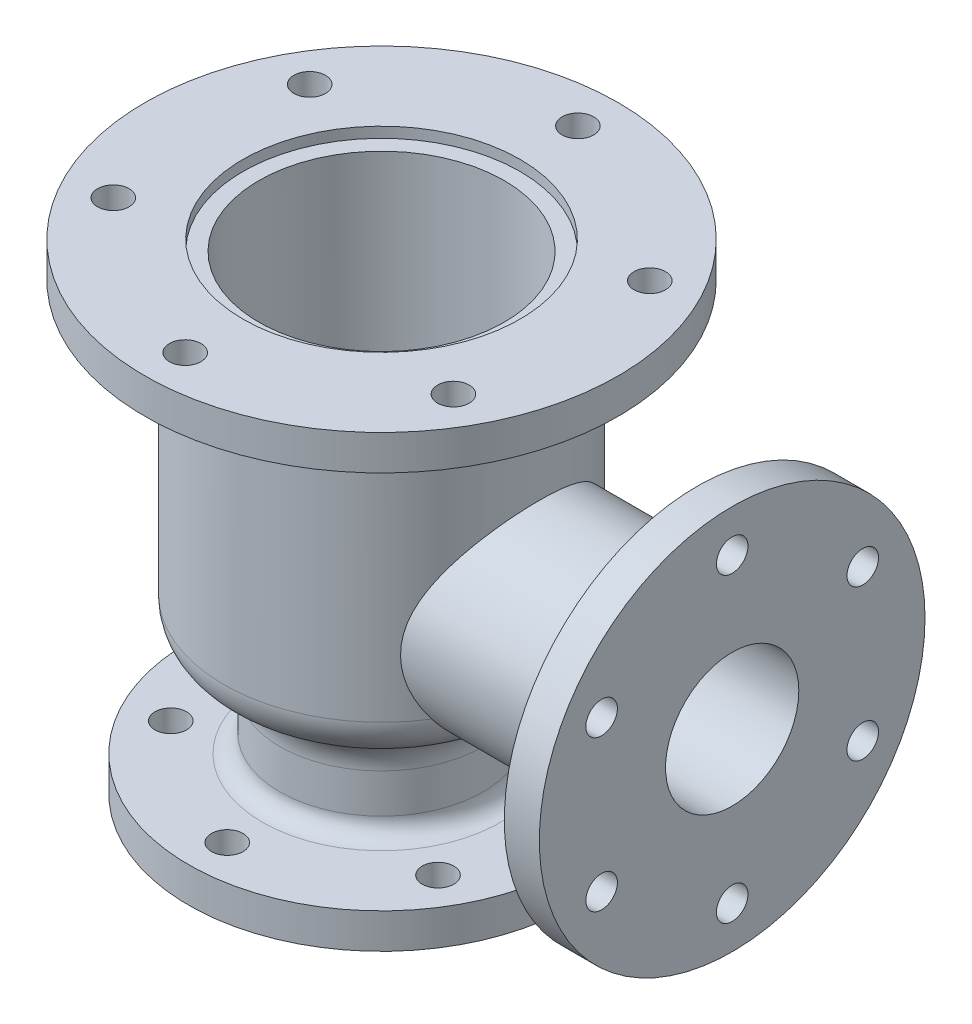
SolidWorks part; units mm, degrees
material "Plain Carbon Steel"
ref_plane "Front Plane" through (0, 0, 0) normal (0, 0, 1) x (1, 0, 0)
ref_plane "Top Plane" through (0, 0, 0) normal (0, 1, 0) x (1, 0, 0)
ref_plane "Right Plane" through (0, 0, 0) normal (1, 0, 0) x (0, 0, -1)
sketch "Sketch1" plane through (0, 0, 0) normal (0, 0, 1) x (1, 0, 0)
  line L0 (0, 0) -> (0, 279.8352) construction
  line L1 (38, 0) -> (110, 0)
  line L2 (110, 0) -> (110, 20)
  line L3 (110, 20) -> (58, 20)
  line L4 (58, 20) -> (58, 74)
  line L5 (90, 74) -> (90, 254)
  line L6 (90, 254) -> (135, 254)
  line L7 (135, 254) -> (135, 274)
  line L8 (135, 274) -> (79, 274)
  line L9 (79, 274) -> (79, 268)
  line L10 (79, 268) -> (70, 268)
  line L11 (70, 268) -> (70, 106)
  line L12 (60, 98) -> (60, 88)
  line L13 (60, 88) -> (46, 88)
  line L14 (46, 88) -> (46, 34)
  line L15 (46, 34) -> (38, 34)
  line L16 (38, 34) -> (38, 0)
  line L17 (58, 74) -> (90, 74)
  line L18 (60, 98) -> (62, 98)
  arc A0 (62, 98) -> (70, 106) centre (62, 106) ccw
  point P9 (70, 98)
  dimension "D4" = 180
  dimension "D6" = 180
  dimension "D7" = 8
  dimension "D1" = 220
  dimension "D2" = 20
  dimension "D3" = 116
  dimension "D5" = 54
  dimension "D9" = 270
  dimension "D10" = 20
  dimension "D11" = 158
  dimension "D12" = 6
  dimension "D13" = 140
  dimension "D14" = 170
  dimension "D16" = 10
  dimension "D17" = 120
  dimension "D18" = 92
  dimension "D19" = 54
  dimension "D20" = 76
revolve "Revolve1" add sketch "Sketch1" angle 360 about L0
ref_plane "Plane1" through (180, 0, 0) normal (1, 0, 0) x (0, 0, -1)
fillet "Fillet3" radius 25 1 edges at (0, 74, -90)
fillet "Fillet4" radius 25 1 edges at (0, 74, -58)
sketch "Sketch2" plane through (180, 0, 0) normal (1, 0, 0) x (0, 0, -1)
  line L0 (0, 0) -> (0, 242.7382) construction
  line L1 (-110, 0) -> (110, 0) construction
  circle A0 centre (0, 132) radius 58
  dimension "D1" = 116
  dimension "D2" = 132
extrude "Boss-Extrude1" add sketch "Sketch2" against normal up to next
sketch "Sketch3" plane through (180, 0, 0) normal (1, 0, 0) x (0, 0, -1)
  circle A0 centre (0, 132) radius 110
  dimension "D1" = 220
extrude "Boss-Extrude2" add sketch "Sketch3" along normal blind 20
sketch "Sketch4" plane through (200, 0, 0) normal (1, 0, 0) x (0, 0, -1)
  circle A0 centre (0, 132) radius 38
  dimension "D1" = 76
extrude "Cut-Extrude1" cut sketch "Sketch4" against normal up to next
sketch "Sketch5" plane through (0, 274, 0) normal (0, 1, 0) x (1, 0, 0)
  line L0 (0, 0) -> (0, 167.0196) construction
  circle A0 centre (0, 112) radius 9
  dimension "D1" = 18
  dimension "D2" = 112
extrude "Cut-Extrude2" cut sketch "Sketch5" against normal up to next (20 mm away)
pattern_circular "CirPattern1" count 6 over 360 about axis through (0, 0, 0) along (0, 1, 0) of "Cut-Extrude2"
sketch "Sketch6" plane through (200, 0, 0) normal (1, 0, 0) x (0, 0, -1)
  line L0 (0, 132) -> (0, 238.5411) construction
  circle A0 centre (0, 218) radius 9
  dimension "D1" = 18
  dimension "D2" = 86
extrude "Cut-Extrude3" cut sketch "Sketch6" against normal up to next (20 mm away)
pattern_circular "CirPattern2" count 6 over 360 about axis through (0, 132, 0) along (1, 0, 0) of "Cut-Extrude3"
sketch "Sketch7" plane through (0, 20, 0) normal (0, 1, 0) x (1, 0, 0)
  line L0 (0, 0) -> (0, 154.0105) construction
  circle A0 centre (0, 88) radius 9
  dimension "D1" = 18
  dimension "D2" = 88
extrude "Cut-Extrude4" cut sketch "Sketch7" against normal up to next (20 mm away)
pattern_circular "CirPattern3" count 6 over 360 about axis through (0, 0, 0) along (0, 1, 0) of "Cut-Extrude4"
fillet "Fillet6" radius 10 1 edges at (0, 20, -58)
